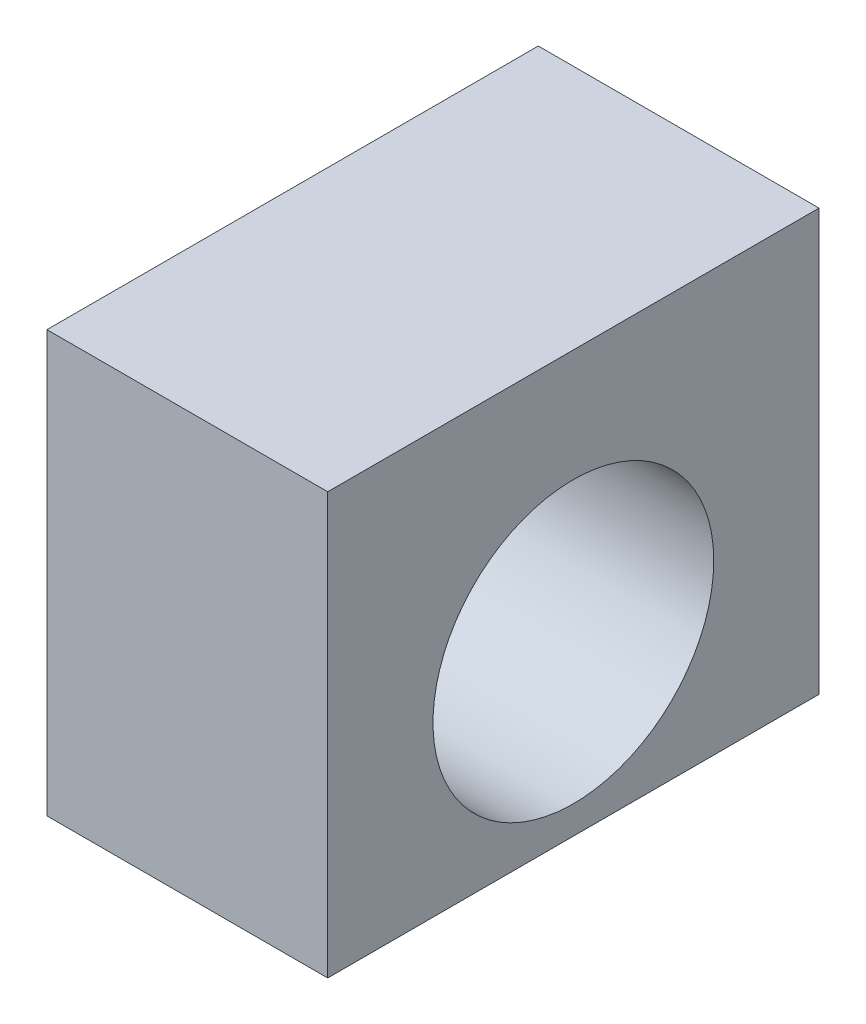
SolidWorks part; units mm, degrees
material "Maple"
ref_plane "Front Plane" through (0, 0, 0) normal (0, 0, 1) x (1, 0, 0)
ref_plane "Top Plane" through (0, 0, 0) normal (0, 1, 0) x (1, 0, 0)
ref_plane "Right Plane" through (0, 0, 0) normal (1, 0, 0) x (0, 0, -1)
sketch "Sketch1" plane through (0, 0, 0) normal (1, 0, 0) x (0, 0, -1)
  line L0 (0, 0) -> (22.225, 0)
  line L1 (0, 0) -> (0, -19.05)
  line L2 (22.225, 0) -> (22.225, -19.05)
  line L3 (0, -19.05) -> (22.225, -19.05)
  line L4 (11.1125, 0) -> (11.1125, -19.05) construction
  circle A0 centre (11.1125, -11.43) radius 6.35
  dimension "D3" = 12.7
  dimension "D1" = 22.225
  dimension "D2" = 19.05
  dimension "D4" = 7.62
extrude "Boss-Extrude1" add sketch "Sketch1" along normal blind 12.7
